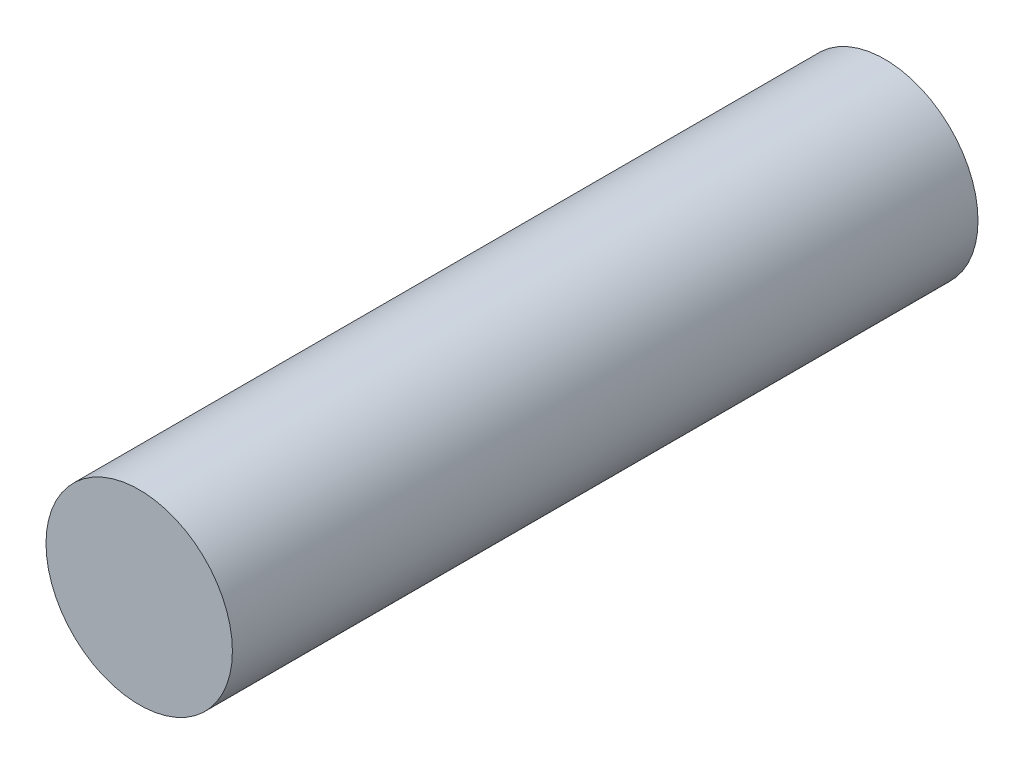
SolidWorks part; units mm, degrees
material "Stainless Steel (ferritic)"
ref_plane "Front Plane" through (0, 0, 0) normal (0, 0, 1) x (1, 0, 0)
ref_plane "Top Plane" through (0, 0, 0) normal (0, 1, 0) x (1, 0, 0)
ref_plane "Right Plane" through (0, 0, 0) normal (1, 0, 0) x (0, 0, -1)
sketch "Sketch1" plane through (0, 0, 0) normal (0, 0, 1) x (1, 0, 0)
  circle A0 centre (0, 0) radius 3.175
  dimension "D1" = 6.35
extrude "Boss-Extrude1" add sketch "Sketch1" along normal mid plane 25.4
